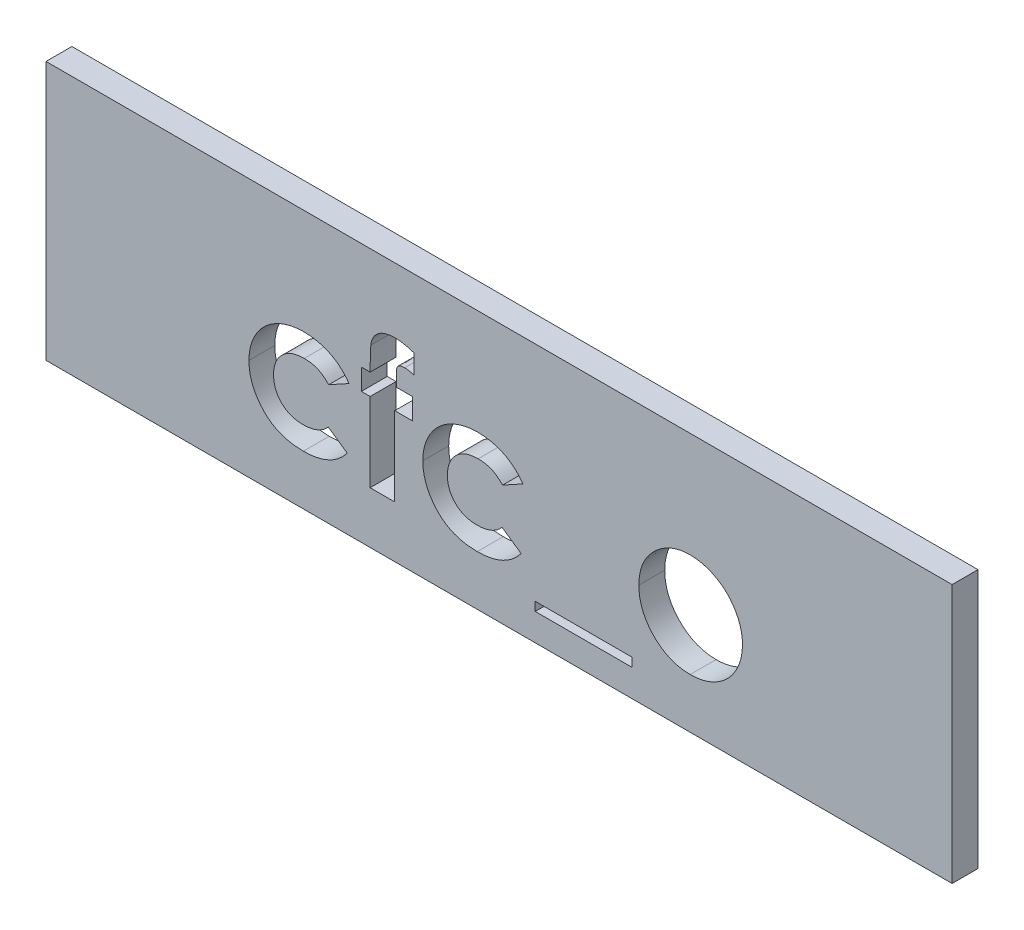
SolidWorks part; units mm, degrees
ref_plane "Plan de face" through (0, 0, 0) normal (0, 0, 1) x (1, 0, 0)
ref_plane "Plan de dessus" through (0, 0, 0) normal (0, 1, 0) x (1, 0, 0)
ref_plane "Plan de droite" through (0, 0, 0) normal (1, 0, 0) x (0, 0, -1)
sketch "Esquisse1" plane through (0, 0, 0) normal (0, 0, 1) x (1, 0, 0)
  line L1 (0, 0) -> (35, 0)
  line L2 (0, 0) -> (0, -10)
  line L3 (0, -10) -> (35, -10)
  line L4 (35, 0) -> (35, -10)
  point P4 (0, 0)
  dimension "D1" = 35
  dimension "D2" = 10
extrude "Boss.-Extru.1" add sketch "Esquisse1" along normal blind 1
sketch "Esquisse2" plane through (0, 0, 0) normal (0, 0, -1) x (-1, 0, 0)
  line L0 (-35, 0) -> (0, 0) construction
  line L1 (-35, -10) -> (-35, 0) construction
  line L2 (0, 0) -> (0, -10) construction
  circle A0 centre (-30, -5) radius 1
  circle A1 centre (-5, -5) radius 1
  dimension "D4" = 2
  dimension "D1" = 5
  dimension "D2" = 5
  dimension "D3" = 5
extrude "Boss.-Extru.2" add sketch "Esquisse2" along normal blind 3
chamfer "Chanfrein1" distance 0.5 angle 45 2 edges at (29, -5, -3) (4, -5, -3)
sketch "Esquisse3" plane through (0, 0, 1) normal (0, 0, 1) x (1, 0, 0)
  line L0 (7.5, -8) -> (27.5, -8) construction
  line L3 (0, -10) -> (35, -10) construction
  line L4 (0, 0) -> (0, -10) construction
  line L5 (35, -10) -> (35, 0) construction
  text T1 "<b>cfc_o</b>" font "Century Gothic" height in points 20
  point P3 (137.8523, -22.7632)
  point P9 (0, 0)
  point P10 (0, 0)
  point P12 (27.5, -8)
  point P13 (136.0675, -22.7632)
  dimension "D1" = 2
  dimension "D2" = 7.5
  dimension "D3" = 20
  dimension "D4" = 7.5
extrude "Enlèv. mat.-Extru.2" cut sketch "Esquisse3" against normal blind 1
